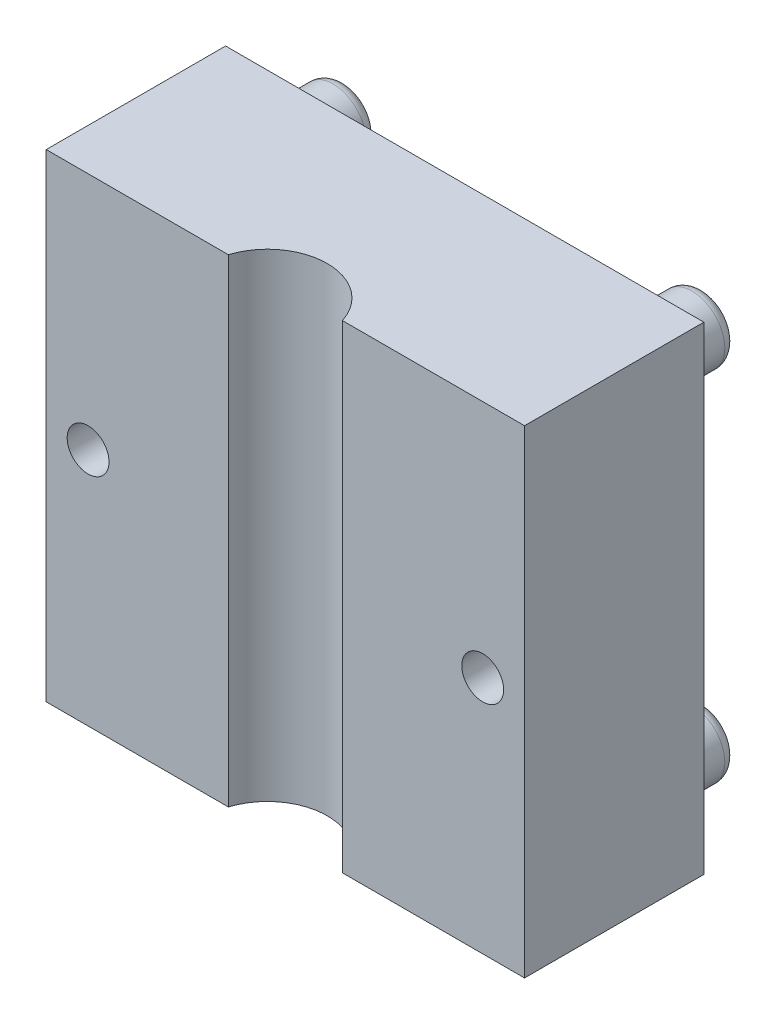
SolidWorks part; units mm, degrees
ref_plane "Front Plane" through (0, 0, 0) normal (0, 0, 1) x (1, 0, 0)
ref_plane "Top Plane" through (0, 0, 0) normal (0, 1, 0) x (1, 0, 0)
ref_plane "Right Plane" through (0, 0, 0) normal (1, 0, 0) x (0, 0, -1)
sketch "Sketch1" plane through (0, 0, 0) normal (0, 0, 1) x (1, 0, 0)
  line L1 (-20, 20) -> (20, 20)
  line L2 (-20, 20) -> (-20, -20)
  line L3 (-20, -20) -> (20, -20)
  line L4 (20, 20) -> (20, -20)
  line L5 (-20, 20) -> (20, -20) construction
  line L6 (-20, -20) -> (20, 20) construction
  point P0 (0, 0)
  dimension "D1" = 40
  dimension "D2" = 40
extrude "Boss-Extrude1" add sketch "Sketch1" along normal blind 15
sketch "Sketch3" plane through (0, 0, 0) normal (0, 0, -1) x (-1, 0, 0)
  line L0 (20, 20) -> (20, -20) construction
  line L1 (20, -20) -> (-20, -20) construction
  line L2 (-20, -20) -> (-20, 20) construction
  line L3 (-20, 20) -> (20, 20) construction
  circle A0 centre (-15, 15) radius 2.75
  circle A1 centre (15, 15) radius 2.75
  circle A2 centre (-15, -15) radius 2.75
  circle A3 centre (15, -15) radius 2.75
  dimension "D1" = 5.5
  dimension "D2" = 5.5
  dimension "D3" = 5.5
  dimension "D4" = 5.5
  dimension "D5" = 5
  dimension "D6" = 5
  dimension "D7" = 5
  dimension "D8" = 5
  dimension "D9" = 5
  dimension "D10" = 5
  dimension "D11" = 5
  dimension "D12" = 5
extrude "Boss-Extrude2" add sketch "Sketch3" along normal blind 5
fillet "Fillet1" radius 1 4 edges at (12.25, -15, -5) (-17.75, -15, -5) (-17.75, 15, -5) (12.25, 15, -5)
sketch "Sketch4" plane through (0, 0, 0) normal (0, 0, -1) x (-1, 0, 0)
  circle A0 centre (0, 0) radius 12.5
  dimension "D1" = 25
extrude "Cut-Extrude1" cut sketch "Sketch4" against normal blind 3.5
sketch "Sketch5" plane through (0, 20, 0) normal (0, 1, 0) x (1, 0, 0)
  line L0 (20, -15) -> (-20, -15) construction
  circle A0 centre (0, -16.5) radius 5
  point P2 (0, -15)
  dimension "D1" = 10
  dimension "D2" = 1.5
extrude "Cut-Extrude2" cut sketch "Sketch5" against normal through all
sketch "Sketch6" plane through (0, 0, 0) normal (0, 0, -1) x (-1, 0, 0)
  line L0 (-20, -20) -> (-20, 20) construction
  line L1 (20, 20) -> (20, -20) construction
  line L3 (-20, 20) -> (20, 20) construction
  circle A0 centre (-16.5, 0) radius 3
  circle A1 centre (16.5, 0) radius 3
  point P4 (-20, 0)
  dimension "D1" = 6
  dimension "D2" = 6
  dimension "D3" = 3.5
  dimension "D4" = 3.5
  dimension "D5" = 20
  dimension "D6" = 20
extrude "Cut-Extrude3" cut sketch "Sketch6" against normal blind 2
sketch "Sketch7" plane through (0, 0, 0) normal (0, 0, -1) x (-1, 0, 0)
  circle A0 centre (16.5, 0) radius 1.75
  circle A1 centre (-16.5, 0) radius 1.75
  dimension "D1" = 3.5
  dimension "D2" = 3.5
extrude "Cut-Extrude4" cut sketch "Sketch7" against normal through all
